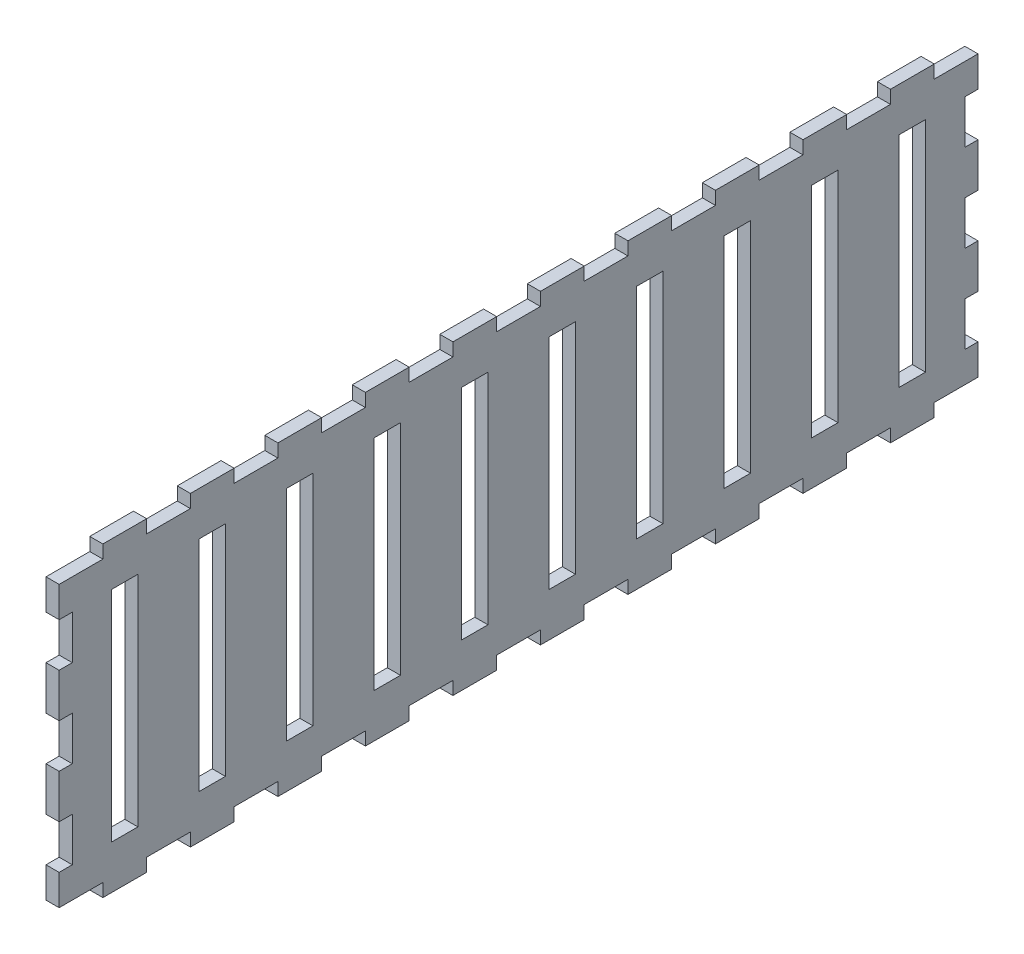
SolidWorks part; units mm, degrees
ref_plane "Front Plane" through (0, 0, 0) normal (0, 0, 1) x (1, 0, 0)
ref_plane "Top Plane" through (0, 0, 0) normal (0, 1, 0) x (1, 0, 0)
ref_plane "Right Plane" through (0, 0, 0) normal (1, 0, 0) x (0, 0, -1)
sketch "Sketch1" plane through (0, 0, 0) normal (1, 0, 0) x (0, 0, -1)
  line L1 (-105, -35) -> (105, -35)
  line L2 (-105, -35) -> (-105, 35)
  line L3 (-105, 35) -> (105, 35)
  line L4 (105, -35) -> (105, 35)
  line L5 (-105, -35) -> (105, 35) construction
  line L6 (-105, 35) -> (105, -35) construction
  point P0 (0, 0)
  dimension "D1" = 210
  dimension "D2" = 70
extrude "Boss-Extrude1" add sketch "Sketch1" along normal blind 3
sketch "Sketch2" plane through (3, 0, 0) normal (1, 0, 0) x (0, 0, -1)
  line L1 (-105, 35) -> (-95, 35)
  line L2 (-105, 35) -> (-105, 32)
  line L3 (-105, 32) -> (-95, 32)
  line L4 (-95, 35) -> (-95, 32)
  dimension "D1" = 10
  dimension "D2" = 3
extrude "Cut-Extrude1" cut sketch "Sketch2" against normal blind 3
pattern_linear "LPattern1" count 11 spacing 20 along (0, 0, -1) of "Cut-Extrude1"
mirror "Mirror1" about plane through (0, 0, 0) normal (0, 1, 0) of "LPattern1", "Cut-Extrude1"
sketch "Sketch3" plane through (3, 0, 0) normal (1, 0, 0) x (0, 0, -1)
  line L0 (-105, 32) -> (-105, -32) construction
  line L1 (-105, 25) -> (-102, 25)
  line L2 (-105, 25) -> (-105, 15)
  line L3 (-105, 15) -> (-102, 15)
  line L4 (-102, 25) -> (-102, 15)
  line L5 (-105, 32) -> (-95, 32) construction
  dimension "D1" = 10
  dimension "D2" = 3
  dimension "D3" = 7
extrude "Cut-Extrude2" cut sketch "Sketch3" against normal blind 3
pattern_linear "LPattern2" count 3 spacing 20 along (0, -1, 0) of "Cut-Extrude2"
mirror "Mirror2" about plane through (0, 0, 0) normal (0, 0, 1) of "LPattern2", "Cut-Extrude2"
sketch "Sketch4" plane through (3, 0, 0) normal (1, 0, 0) x (0, 0, -1)
  line L0 (-105, 15) -> (-105, 5) construction
  line L1 (-93, 25) -> (-87, 25)
  line L2 (-93, 25) -> (-93, -25)
  line L3 (-93, -25) -> (-87, -25)
  line L4 (-87, 25) -> (-87, -25)
  line L5 (-85, 35) -> (-95, 35) construction
  dimension "D1" = 50
  dimension "D2" = 6
  dimension "D3" = 12
  dimension "D4" = 10
extrude "Cut-Extrude3" cut sketch "Sketch4" against normal blind 3
pattern_linear "LPattern3" count 10 spacing 20 along (0, 0, -1) of "Cut-Extrude3"
